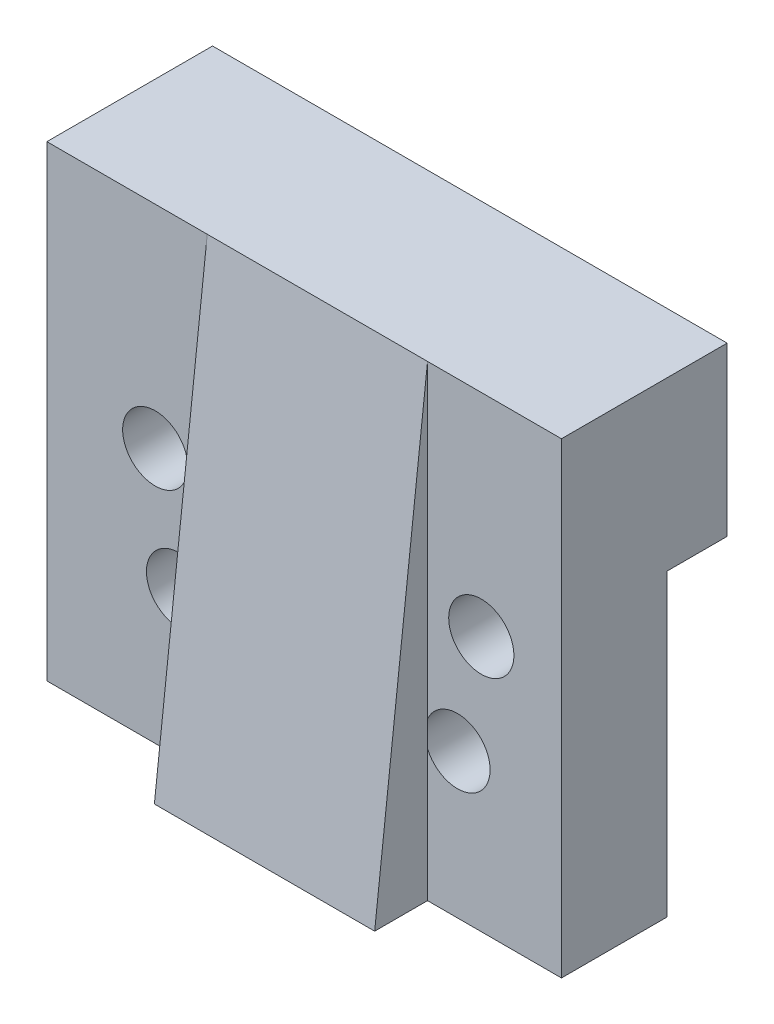
SolidWorks part; units mm, degrees
ref_plane "Front Plane" through (0, 0, 0) normal (0, 0, 1) x (1, 0, 0)
ref_plane "Top Plane" through (0, 0, 0) normal (0, 1, 0) x (1, 0, 0)
ref_plane "Right Plane" through (0, 0, 0) normal (1, 0, 0) x (0, 0, -1)
sketch "Sketch1" plane through (0, 0, 0) normal (0, 0, 1) x (1, 0, 0)
  line L0 (-16.2301, 8.75) -> (-16.2301, -1.75)
  line L1 (-16.2301, -7) -> (12.9699, -7) construction
  line L2 (5.3699, -14.75) -> (-7.0301, -14.75) construction
  line L3 (-16.2301, -7) -> (-16.2301, -17.75)
  line L4 (12.9699, 8.75) -> (12.9699, -1.75)
  line L5 (-16.2301, -1.75) -> (-16.2301, -7)
  line L6 (-16.2301, -1.75) -> (12.9699, -1.75) construction
  line L7 (12.9699, 8.75) -> (-16.2301, 8.75)
  line L8 (12.9699, -7) -> (12.9699, -17.75)
  line L9 (-16.2301, 3.5) -> (-13.3301, 3.5) construction
  line L10 (-13.3301, -1.75) -> (-13.3301, 8.75) construction
  line L11 (-13.3301, 3.5) -> (11.6699, 3.5) construction
  line L12 (11.6699, -1.75) -> (11.6699, 8.75) construction
  line L13 (-0.8301, 3.5) -> (-0.8301, -30.2755) construction
  line L14 (12.9699, -7) -> (12.9699, -1.75)
  line L17 (-16.2301, -17.75) -> (12.9699, -17.75)
  line L18 (-7.0301, -7) -> (-7.0301, -12.1) construction
  line L19 (-7.0301, -9.55) -> (-8.7301, -9.55) construction
  circle A0 centre (-10.0801, -3.25) radius 1
  circle A1 centre (8.4199, -3.25) radius 1
  circle A2 centre (-8.7301, -9.55) radius 1
  circle A3 centre (7.0699, -9.55) radius 1
  point P22 (-0.8301, -14.75)
  dimension "D1" = 2
  dimension "D6" = 5.1
  dimension "D8" = 2
  dimension "D2" = 29.2
  dimension "D3" = 12
  dimension "D4" = 10.75
  dimension "D7" = 1.7
  dimension "D9" = 10.5
  dimension "D10" = 9.25
extrude "Boss-Extrude2" add sketch "Sketch1" along normal blind 1.7
sketch "Sketch2" plane through (0, 0, 1.7) normal (0, 0, 1) x (1, 0, 0)
  line L0 (-16.2301, 8.75) -> (-16.2301, -1.75)
  line L1 (-16.2301, -7) -> (12.9699, -7) construction
  line L2 (5.3699, -14.75) -> (-7.0301, -14.75) construction
  line L3 (-16.2301, -7) -> (-16.2301, -17.75)
  line L4 (12.9699, 8.75) -> (12.9699, -1.75)
  line L5 (-16.2301, -1.75) -> (-16.2301, -7)
  line L6 (-16.2301, -1.75) -> (12.9699, -1.75) construction
  line L7 (12.9699, 8.75) -> (-16.2301, 8.75)
  line L8 (12.9699, -7) -> (12.9699, -17.75)
  line L9 (-16.2301, 3.5) -> (-13.3301, 3.5) construction
  line L10 (-13.3301, -1.75) -> (-13.3301, 8.75) construction
  line L11 (-13.3301, 3.5) -> (11.6699, 3.5) construction
  line L12 (11.6699, -1.75) -> (11.6699, 8.75) construction
  line L13 (-0.8301, 3.5) -> (-0.8301, -30.2755) construction
  line L14 (12.9699, -7) -> (12.9699, -1.75)
  line L15 (-16.2301, -17.75) -> (12.9699, -17.75)
  line L16 (-7.0301, -7) -> (-7.0301, -12.1) construction
  line L17 (-7.0301, -9.55) -> (-8.7301, -9.55) construction
  circle A0 centre (-10.0801, -3.25) radius 1.85
  circle A1 centre (8.4199, -3.25) radius 1.85
  circle A2 centre (-8.7301, -9.55) radius 1.85
  circle A3 centre (7.0699, -9.55) radius 1.85
  point P20 (-0.8301, -14.75)
  dimension "D1" = 3.7
  dimension "D8" = 10.5
  dimension "D6" = 3.7
  dimension "D2" = 29.2
  dimension "D3" = 12
  dimension "D4" = 5.1
  dimension "D5" = 1.7
  dimension "D7" = 10.75
  dimension "D9" = 9.25
extrude "Boss-Extrude3" add sketch "Sketch2" along normal blind 4.3
sketch "Sketch3" plane through (0, 0, 0) normal (0, 0, -1) x (-1, 0, 0)
  line L0 (-3.8699, -7) -> (5.5301, -7)
  line L1 (7.0301, -5.5) -> (7.0301, -0.75)
  line L3 (-12.9699, 8.75) -> (-12.9699, -0.75)
  line L4 (7.0301, -0.75) -> (16.2301, -0.75)
  line L5 (16.2301, 8.75) -> (-12.9699, 8.75)
  line L6 (-12.9699, -0.75) -> (-5.3699, -0.75)
  line L7 (16.2301, 8.75) -> (16.2301, -1.75) construction
  line L8 (16.2301, -0.75) -> (16.2301, 8.75)
  line L9 (-5.3699, -0.75) -> (-5.3699, -5.5)
  line L10 (0.8301, -2.7753) -> (0.8301, -7) construction
  line L12 (0.8301, 3.5) -> (0.8301, -30.2755) construction
  line L13 (5.5301, -7) -> (7.0301, -5.5)
  line L16 (-3.8699, -7) -> (-5.3699, -5.5)
extrude "Boss-Extrude4" add sketch "Sketch3" along normal blind 3.4
sketch "Sketch4" plane through (5.3699, 0, 0) normal (1, 0, 0) x (0, 0, -1)
  line L0 (-6, -17.75) -> (-6, 8.75)
  line L1 (-6, -17.75) -> (-9, -17.75)
  line L2 (-9, -17.75) -> (-6, 8.75)
extrude "Boss-Extrude5" add sketch "Sketch4" against normal blind 12.5
